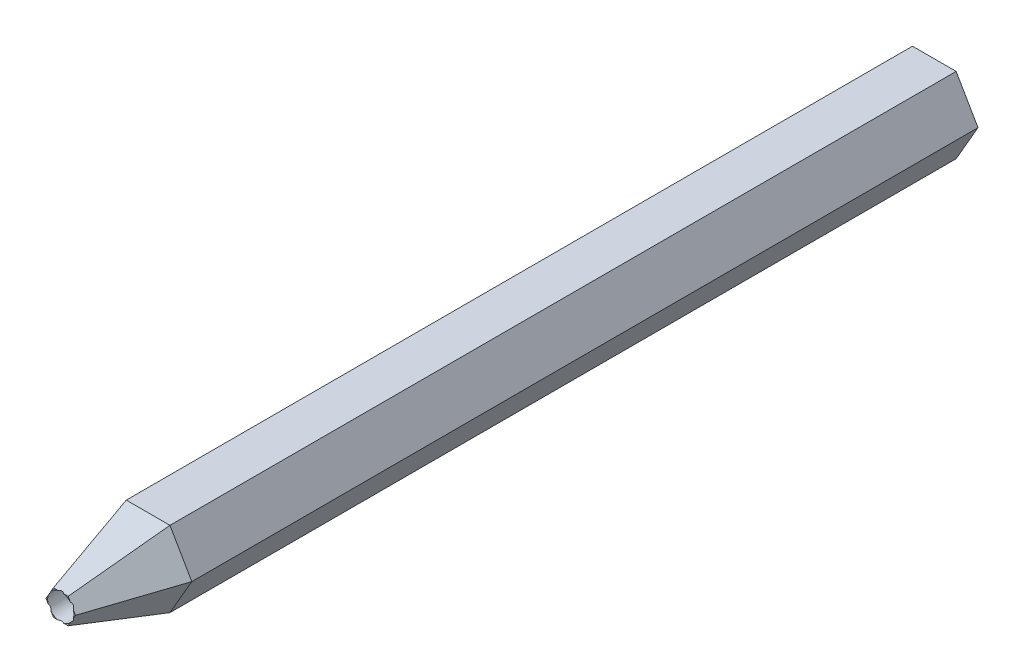
SolidWorks part; units mm, degrees
ref_plane "Přední rovina" through (0, 0, 0) normal (0, 0, 1) x (1, 0, 0)
ref_plane "Horní rovina" through (0, 0, 0) normal (0, 1, 0) x (1, 0, 0)
ref_plane "Pravá rovina" through (0, 0, 0) normal (1, 0, 0) x (0, 0, -1)
sketch "Skica1" plane through (0, 0, 0) normal (0, 0, 1) x (1, 0, 0)
  line L1 (2.5, -4.3301) -> (5, 0)
  line L2 (5, 0) -> (2.5, 4.3301)
  line L3 (2.5, 4.3301) -> (-2.5, 4.3301)
  line L4 (-2.5, 4.3301) -> (-5, 0)
  line L5 (-5, 0) -> (-2.5, -4.3301)
  line L6 (-2.5, -4.3301) -> (2.5, -4.3301)
  circle A0 centre (0, 0) radius 4.3301 construction
  dimension "D1" = 5
extrude "Vysunout1" add sketch "Skica1" along normal blind 100
chamfer "Zkosit2" distance 10 angle 16 6 edges at (-3.75, -2.1651, 100) (-3.75, 2.1651, 100) (0, 4.3301, 100) (3.75, 2.1651, 100) (3.75, -2.1651, 100) (0, -4.3301, 100)
sketch "Skica2" plane through (0, 0, 100) normal (0, 0, 1) x (1, 0, 0)
  circle A0 centre (0, 0) radius 1.5
  dimension "D1" = 3
extrude "Odebrat vysunutím1" cut sketch "Skica2" against normal through all
